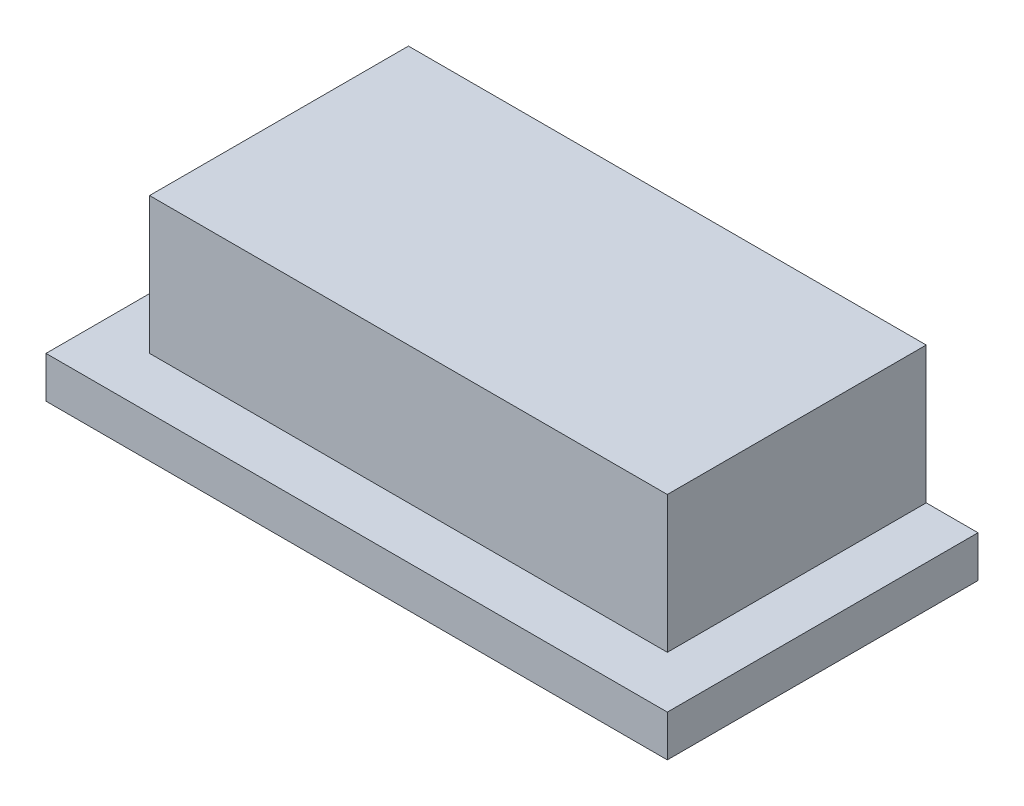
SolidWorks part; units mm, degrees
ref_plane "Спереди" through (0, 0, 0) normal (0, 0, 1) x (1, 0, 0)
ref_plane "Сверху" through (0, 0, 0) normal (0, 1, 0) x (1, 0, 0)
ref_plane "Справа" through (0, 0, 0) normal (1, 0, 0) x (0, 0, -1)
sketch "Эскиз1" plane through (0, 0, 0) normal (0, 1, 0) x (1, 0, 0)
  line L1 (300, 197.243) -> (-300, 197.243)
  line L2 (300, 197.243) -> (300, -102.757)
  line L3 (300, -102.757) -> (-300, -102.757)
  line L4 (-300, 197.243) -> (-300, -102.757)
  line L5 (300, 197.243) -> (-300, -102.757) construction
  line L6 (300, -102.757) -> (-300, 197.243) construction
  point P0 (0, 47.243)
  dimension "D1" = 600
  dimension "D2" = 300
extrude "Бобышка-Вытянуть1" add sketch "Эскиз1" along normal blind 40
sketch "Эскиз2" plane through (0, 40, 0) normal (0, 1, 0) x (1, 0, 0)
  line L0 (300, 197.243) -> (-300, 197.243) construction
  line L1 (-250, 197.243) -> (250, 197.243)
  line L2 (-250, 197.243) -> (-250, -52.757)
  line L3 (-250, -52.757) -> (250, -52.757)
  line L4 (250, 197.243) -> (250, -52.757)
  line L5 (250, -52.757) -> (300, -52.757) construction
  line L6 (300, -102.757) -> (300, 197.243) construction
  line L7 (-250, -52.757) -> (-300, -52.757) construction
  line L8 (-300, 197.243) -> (-300, -102.757) construction
  dimension "D1" = 50
  dimension "D2" = 250
extrude "Бобышка-Вытянуть2" add sketch "Эскиз2" along normal blind 132
